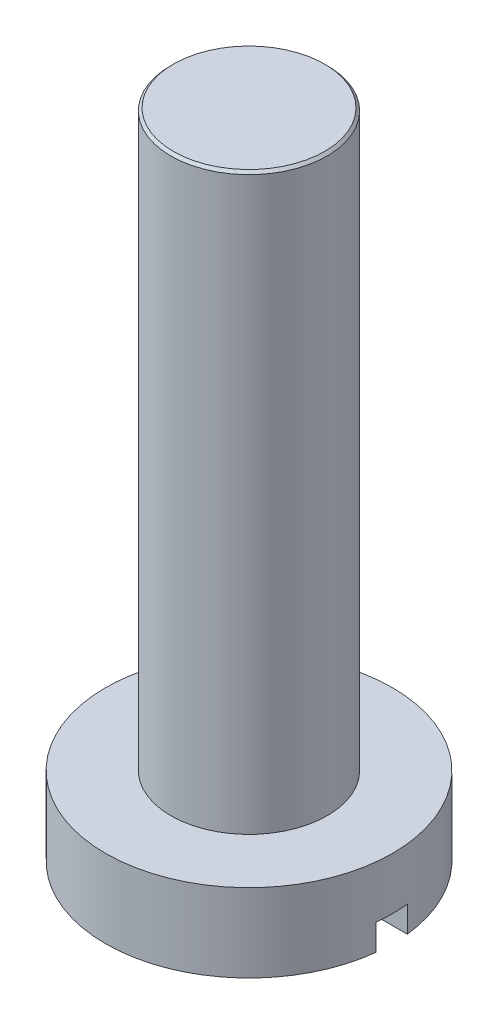
SolidWorks part; units mm, degrees
ref_plane "Front Plane" through (0, 0, 0) normal (0, 0, 1) x (1, 0, 0)
ref_plane "Top Plane" through (0, 0, 0) normal (0, 1, 0) x (1, 0, 0)
ref_plane "Right Plane" through (0, 0, 0) normal (1, 0, 0) x (0, 0, -1)
sketch "Sketch1" plane through (0, 0, 0) normal (0, 1, 0) x (1, 0, 0)
  circle A0 centre (0, 0) radius 1.5
  dimension "D1" = 3
extrude "Boss-Extrude1" add sketch "Sketch1" along normal blind 11
cosmetic thread "Cosmetic Thread1" parameters "D1"=11, "D2"=2.439
sketch "Sketch2" plane through (0, 0, 0) normal (0, -1, 0) x (1, 0, 0)
  circle A0 centre (0, 0) radius 2.75
  circle A1 centre (0, 0) radius 1.5
  circle A2 centre (0, 0) radius 1.5 construction
  dimension "D1" = 0
  dimension "D2" = 1.25
extrude "Boss-Extrude2" add sketch "Sketch2" along normal blind 1.5 separate body
sketch "Sketch3" plane through (0, -1.5, 0) normal (0, -1, 0) x (1, 0, 0)
  line L1 (-4.0982, -0.3) -> (4.0982, -0.3)
  line L2 (-4.0982, -0.3) -> (-4.0982, 0.3)
  line L3 (-4.0982, 0.3) -> (4.0982, 0.3)
  line L4 (4.0982, -0.3) -> (4.0982, 0.3)
  line L5 (-4.0982, -0.3) -> (4.0982, 0.3) construction
  line L6 (-4.0982, 0.3) -> (4.0982, -0.3) construction
  point P0 (0, 0)
  dimension "D1" = 0.6
extrude "Cut-Extrude1" cut sketch "Sketch3" against normal blind 0.5
chamfer "Chamfer1" distance 0.05 angle 45 1 edges at (0, 11, 1.5)
